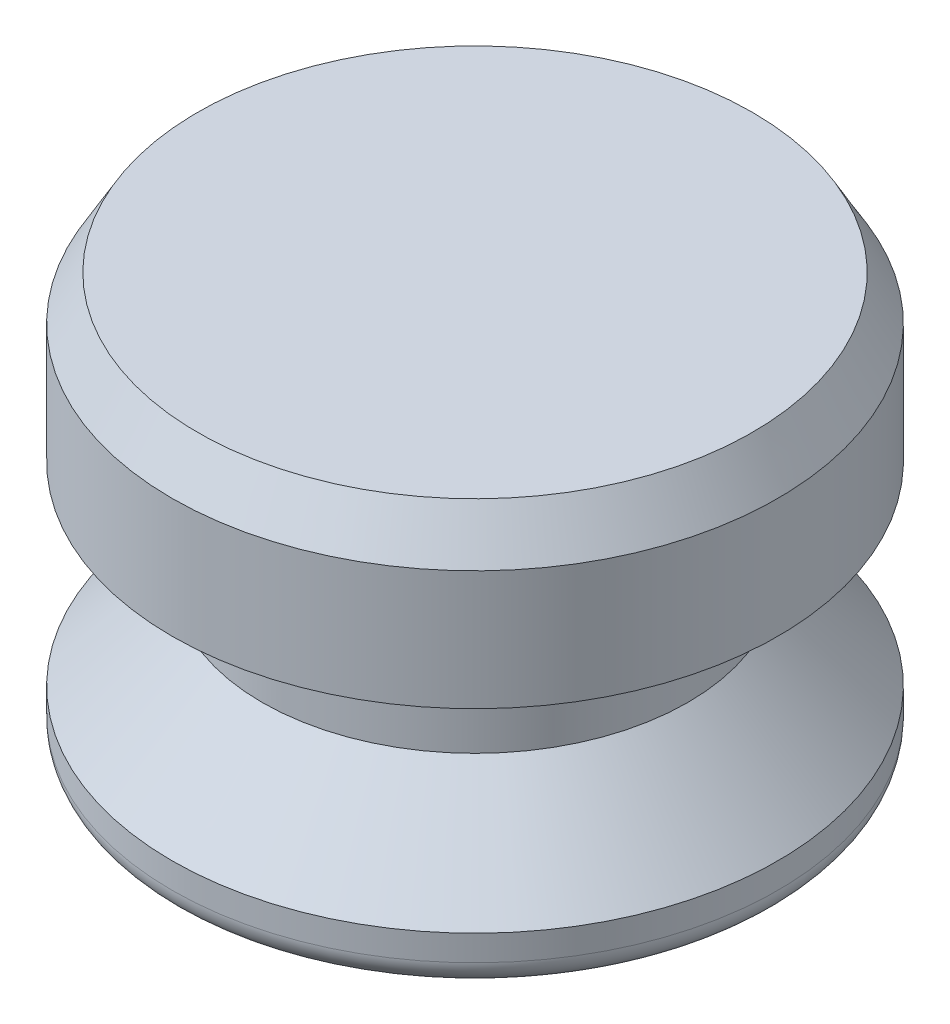
SolidWorks part; units mm, degrees
ref_plane "Front Plane" through (0, 0, 0) normal (0, 0, 1) x (1, 0, 0)
ref_plane "Top Plane" through (0, 0, 0) normal (0, 1, 0) x (1, 0, 0)
ref_plane "Right Plane" through (0, 0, 0) normal (1, 0, 0) x (0, 0, -1)
sketch "Sketch1" plane through (0, 0, 0) normal (0, 0, 1) x (1, 0, 0)
  line L0 (0, 0) -> (0, 12.7) construction
  line L1 (0, 0) -> (-9.398, 0)
  line L2 (-9.398, 0) -> (-9.398, 1.5875)
  line L4 (-6.604, 4.445) -> (-6.604, 7.62)
  line L5 (-6.604, 7.62) -> (-9.398, 7.62)
  line L6 (-9.398, 7.62) -> (-9.398, 12.7)
  line L7 (-9.398, 12.7) -> (0, 12.7)
  line L8 (-9.525, 16.6801) -> (-9.525, -9.6051) construction
  line L9 (0, 0) -> (0, 12.7)
  line L10 (-6.604, 4.445) -> (-9.398, 1.5875)
  dimension "D1" = 12.7
  dimension "D2" = 9.398
  dimension "D3" = 3.175
  dimension "D4" = 1.5875
  dimension "D5" = 9.525
  dimension "D6" = 6.604
  dimension "D7" = 7.62
revolve "Revolve1" add sketch "Sketch1" angle 360 about L9
fillet "Fillet1" radius 0.7937 1 edges at (0, 0, -9.398)
chamfer "Chamfer1" distance 0.7937 angle 60 1 edges at (0, 12.7, -9.398)
